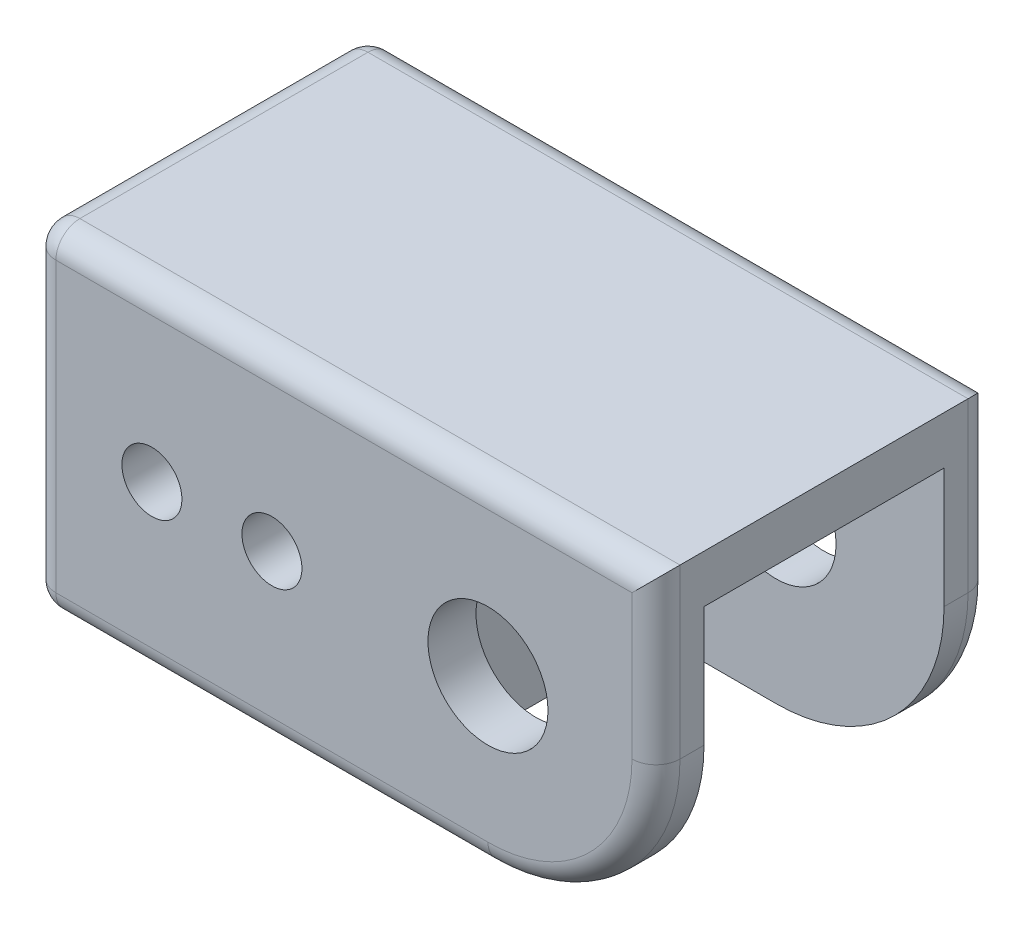
SolidWorks part; units mm, degrees
ref_plane "Front Plane" through (0, 0, 0) normal (0, 0, 1) x (1, 0, 0)
ref_plane "Top Plane" through (0, 0, 0) normal (0, 1, 0) x (1, 0, 0)
ref_plane "Right Plane" through (0, 0, 0) normal (1, 0, 0) x (0, 0, -1)
sketch "Sketch1" plane through (0, 0, 0) normal (0, 0, 1) x (1, 0, 0)
  line L1 (17.78, 17.78) -> (17.78, -17.78)
  line L2 (-48.26, 17.78) -> (-48.26, -17.78)
  line L3 (-48.26, -17.78) -> (17.78, -17.78)
  line L4 (-48.26, 17.78) -> (17.78, 17.78)
  circle A0 centre (0, 0) radius 6.35
  circle A1 centre (-35.56, 0) radius 3.175
  circle A2 centre (-22.86, 0) radius 3.175
  point P0 (-48.26, 0)
  point P2 (17.78, 0)
  dimension "D4" = 12.7
  dimension "D5" = 6.35
  dimension "D7" = 6.35
  dimension "D1" = 35.56
  dimension "D2" = 17.78
  dimension "D3" = 66.04
  dimension "D6" = 12.7
  dimension "D8" = 25.4
extrude "Boss-Extrude1" add sketch "Sketch1" along normal blind 35.56
ref_plane "Plane1" through (0, 0, 17.78) normal (0, 0, 1) x (1, 0, 0)
sketch "Sketch2" plane through (0, 0, 17.78) normal (0, 0, 1) x (1, 0, 0)
  line L0 (0, 12.7) -> (17.78, 12.7)
  line L1 (17.78, -17.78) -> (17.78, 17.78) construction
  line L2 (17.78, 12.7) -> (17.78, -17.78)
  line L3 (17.78, -17.78) -> (-12.7, -17.78)
  line L4 (-48.26, -17.78) -> (17.78, -17.78) construction
  line L5 (-12.7, -17.78) -> (-12.7, 0)
  arc A0 (0, 12.7) -> (-12.7, 0) centre (0, 0) ccw
  dimension "D1" = 25.4
extrude "Cut-Extrude1" cut sketch "Sketch2" against normal blind 12.7 and the other way blind 12.7
sketch "Sketch3" plane through (-48.26, 0, 0) normal (-1, 0, 0) x (0, 0, 1)
  line L0 (35.56, 17.78) -> (0, 17.78) construction
  line L1 (5.08, 12.7) -> (30.48, 12.7)
  line L2 (5.08, 12.7) -> (5.08, -12.7)
  line L3 (5.08, -12.7) -> (30.48, -12.7)
  line L4 (30.48, 12.7) -> (30.48, -12.7)
  line L5 (5.08, 12.7) -> (30.48, -12.7) construction
  line L6 (5.08, -12.7) -> (30.48, 12.7) construction
  point P0 (17.78, 0)
  point P10 (17.78, 17.78)
  dimension "D1" = 25.4
  dimension "D2" = 25.4
extrude "Cut-Extrude2" cut sketch "Sketch3" against normal blind 33.02
fillet "Fillet1" radius 17.78 2 edges at (17.78, -17.78, 33.02) (17.78, -17.78, 2.54)
fillet "Fillet2" radius 2.54 12 edges at (17.78, 8.89, 35.56) (12.5724, -12.5724, 35.56) (17.78, 8.89, 0) (12.5724, -12.5724, 0) (-24.13, -17.78, 35.56) (-24.13, -17.78, 0) (-48.26, -17.78, 17.78) (-48.26, 0, 0) (-15.24, 17.78, 0) (-48.26, 17.78, 17.78) (-48.26, 0, 35.56) (-15.24, 17.78, 35.56)
